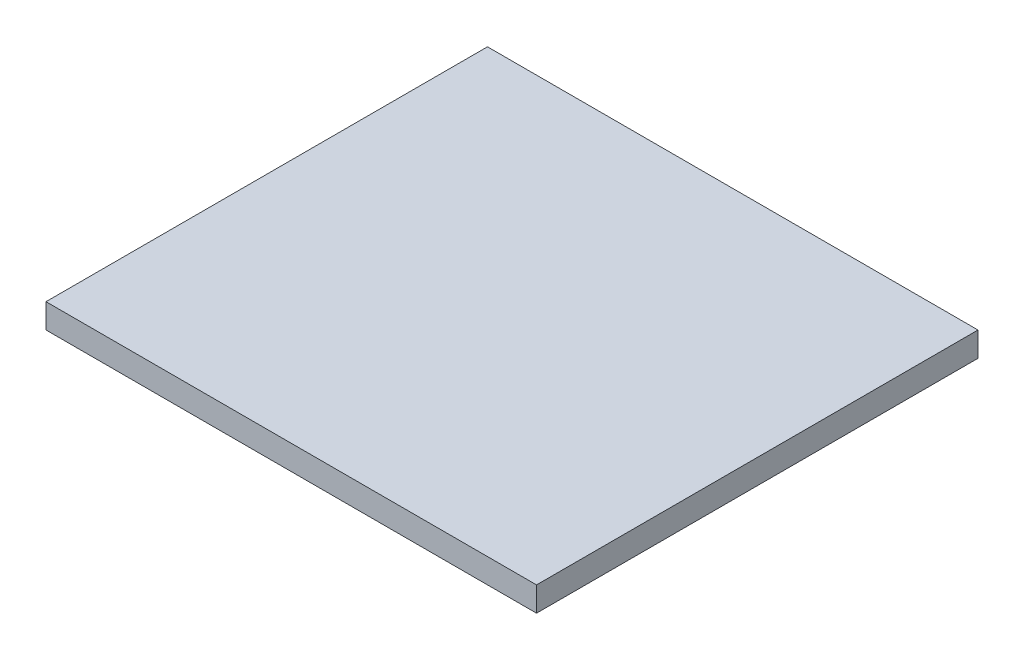
SolidWorks part; units mm, degrees
ref_plane "Front Plane" through (0, 0, 0) normal (0, 0, 1) x (1, 0, 0)
ref_plane "Top Plane" through (0, 0, 0) normal (0, 1, 0) x (1, 0, 0)
ref_plane "Right Plane" through (0, 0, 0) normal (1, 0, 0) x (0, 0, -1)
sketch "Sketch1" plane through (0, 0, 0) normal (0, 1, 0) x (1, 0, 0)
  line L1 (0, 0) -> (20, 0)
  line L2 (0, 0) -> (0, 18)
  line L3 (0, 18) -> (20, 18)
  line L4 (20, 0) -> (20, 18)
  dimension "D1" = 20
  dimension "D2" = 18
extrude "Boss-Extrude1" add sketch "Sketch1" along normal blind 1
